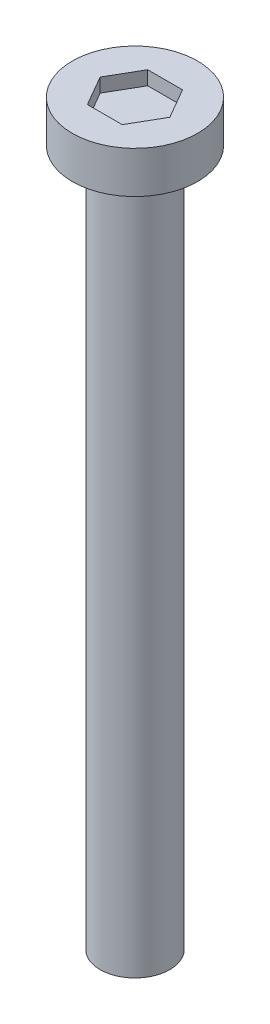
SolidWorks part; units mm, degrees
ref_plane "Front Plane" through (0, 0, 0) normal (0, 0, 1) x (1, 0, 0)
ref_plane "Top Plane" through (0, 0, 0) normal (0, 1, 0) x (1, 0, 0)
ref_plane "Right Plane" through (0, 0, 0) normal (1, 0, 0) x (0, 0, -1)
sketch "Sketch1" plane through (0, 0, 0) normal (0, 1, 0) x (1, 0, 0)
  circle A0 centre (0, 0) radius 1.25
  dimension "D1" = 2.5
extrude "Boss-Extrude1" add sketch "Sketch1" along normal blind 25
sketch "Sketch4" plane through (0, 25, 0) normal (0, 1, 0) x (1, 0, 0)
  circle A0 centre (0, 0) radius 2.25
  dimension "D1" = 4.5
extrude "Boss-Extrude2" add sketch "Sketch4" along normal blind 1.5
sketch "Sketch5" plane through (0, 26.5, 0) normal (0, 1, 0) x (1, 0, 0)
  line L1 (1.25, 0) -> (0.625, 1.0825)
  line L2 (0.625, 1.0825) -> (-0.625, 1.0825)
  line L3 (-0.625, 1.0825) -> (-1.25, 0)
  line L4 (-1.25, 0) -> (-0.625, -1.0825)
  line L5 (-0.625, -1.0825) -> (0.625, -1.0825)
  line L6 (0.625, -1.0825) -> (1.25, 0)
  circle A0 centre (0, 0) radius 1.0825 construction
  dimension "D1" = 1.25
extrude "Cut-Extrude1" cut sketch "Sketch5" against normal blind 0.5
thread "Thread1" pitch 0.7 start angle 0, offset 0, length 24, pitch 0.7, diameter 2.5
ref_plane "Plane1" through (1.25, 0, 0) normal (0, 0, 1) x (1, 0, 0)
sketch "Thread Profile1" plane through (1.25, 0, 0) normal (0, 0, 1) x (1, 0, 0)
  line L0 (0, 0) -> (0, 0.7) construction
  line L1 (0, 0) -> (0.3789, 0.2187)
  line L2 (0.3789, 0.2187) -> (0.3789, 0.3062)
  line L3 (0.3789, 0.3062) -> (0, 0.525)
  line L4 (0.3789, 0.2625) -> (0, 0.2625) construction
  line L11 (0, 0) -> (0, 0.525)
  point P2 (0, 0)
  dimension "Pitch" = 0.7
  dimension "Profile_Angle" = 60
  dimension "Profile_Land" = 0.0875
  dimension "Profile_Height" = 0.3789
